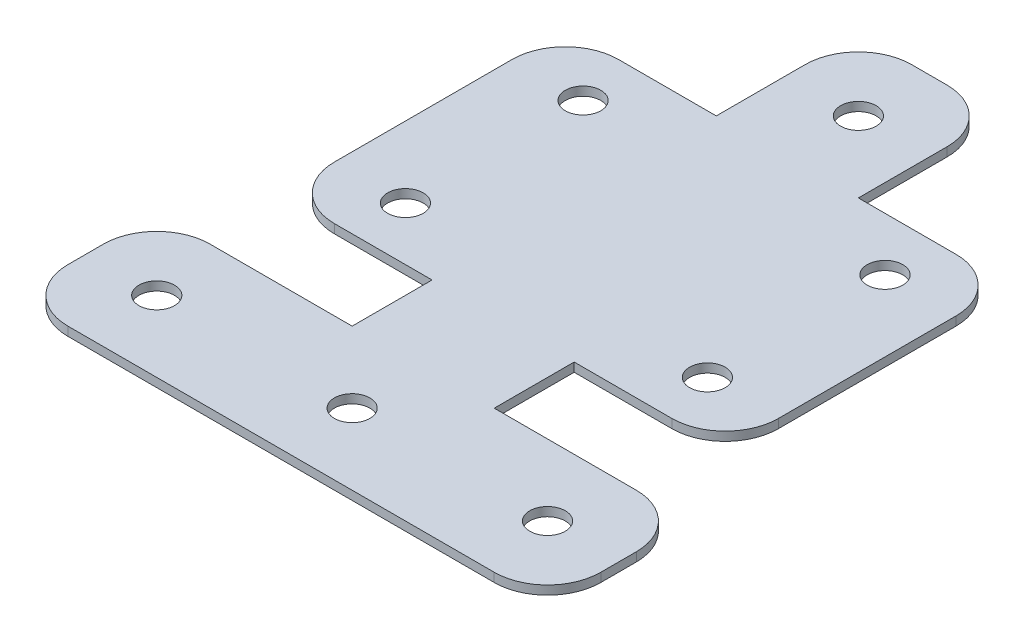
SolidWorks part; units mm, degrees
ref_plane "Front Plane" through (0, 0, 0) normal (0, 0, 1) x (1, 0, 0)
ref_plane "Top Plane" through (0, 0, 0) normal (0, 1, 0) x (1, 0, 0)
ref_plane "Right Plane" through (0, 0, 0) normal (1, 0, 0) x (0, 0, -1)
sketch "Sketch1" plane through (0, 0, 0) normal (0, 1, 0) x (1, 0, 0)
  line L0 (12.7, 12.7) -> (14.2875, 12.7)
  line L1 (-12.7, -12.7) -> (12.7, -12.7)
  line L2 (-12.7, -12.7) -> (-12.7, 12.7) construction
  line L3 (-12.7, 12.7) -> (12.7, 12.7) construction
  line L4 (12.7, -12.7) -> (12.7, 12.7) construction
  line L5 (-12.7, -12.7) -> (12.7, 12.7) construction
  line L6 (-12.7, 12.7) -> (12.7, -12.7) construction
  line L7 (22.225, 12.7) -> (47.625, 12.7)
  line L8 (47.625, 12.7) -> (47.625, -12.7)
  line L9 (47.625, -12.7) -> (22.225, -12.7)
  line L10 (22.225, -12.7) -> (12.7, -12.7)
  line L11 (22.225, 12.7) -> (22.225, -12.7) construction
  line L12 (-12.7, -12.7) -> (-22.225, -12.7)
  line L13 (-22.225, -12.7) -> (-22.225, 12.7) construction
  line L14 (-22.225, 12.7) -> (-12.7, 12.7)
  line L15 (-22.225, 12.7) -> (-47.625, 12.7)
  line L16 (-47.625, 12.7) -> (-47.625, -12.7)
  line L17 (-47.625, -12.7) -> (-22.225, -12.7)
  line L18 (-47.625, 12.7) -> (-22.225, -12.7) construction
  line L19 (-47.625, -12.7) -> (-22.225, 12.7) construction
  line L20 (22.225, 12.7) -> (47.625, -12.7) construction
  line L21 (22.225, -12.7) -> (47.625, 12.7) construction
  line L22 (-12.7, 12.7) -> (-12.7, 25.4)
  line L23 (-12.7, 26.9875) -> (12.7, 26.9875) construction
  line L24 (-12.7, 25.4) -> (12.7, 25.4) construction
  line L25 (-12.7, 26.9875) -> (-12.7, 77.7875) construction
  line L26 (-12.7, 77.7875) -> (12.7, 77.7875) construction
  line L27 (12.7, 77.7875) -> (12.7, 26.9875) construction
  line L28 (-12.7, 77.7875) -> (-12.7, 103.1875)
  line L29 (-12.7, 103.1875) -> (12.7, 103.1875)
  line L30 (12.7, 103.1875) -> (12.7, 77.7875)
  line L31 (12.7, 77.7875) -> (14.2875, 77.7875)
  line L32 (14.2875, 77.7875) -> (14.2875, 26.9875) construction
  line L33 (14.2875, 26.9875) -> (12.7, 26.9875)
  line L34 (14.2875, 26.9875) -> (39.6875, 26.9875)
  line L35 (39.6875, 26.9875) -> (39.6875, 77.7875)
  line L36 (39.6875, 77.7875) -> (14.2875, 77.7875)
  line L37 (26.9875, 77.7875) -> (26.9875, 26.9875) construction
  line L38 (-12.7, 26.9875) -> (-14.2875, 26.9875)
  line L39 (-14.2875, 26.9875) -> (-14.2875, 77.7875) construction
  line L40 (-14.2875, 77.7875) -> (-12.7, 77.7875)
  line L41 (-14.2875, 77.7875) -> (-39.6875, 77.7875)
  line L42 (-39.6875, 77.7875) -> (-39.6875, 26.9875)
  line L43 (-39.6875, 26.9875) -> (-14.2875, 26.9875)
  line L44 (-26.9875, 77.7875) -> (-26.9875, 26.9875) construction
  line L45 (12.7, 25.4) -> (12.7, 12.7)
  line L46 (-12.7, 25.4) -> (-12.7, 26.9875)
  line L47 (12.7, 26.9875) -> (12.7, 25.4)
  line L48 (14.2875, 12.7) -> (14.2875, -12.7) construction
  line L49 (20.6375, 12.7) -> (20.6375, -12.7) construction
  line L50 (14.2875, 12.7) -> (20.6375, 12.7)
  line L51 (20.6375, 12.7) -> (22.225, 12.7)
  line L52 (-12.7, 103.1875) -> (12.7, 77.7875) construction
  line L53 (12.7, 103.1875) -> (-12.7, 77.7875) construction
  circle A0 centre (26.9875, 36.5125) radius 3.175
  circle A1 centre (26.9875, 68.2625) radius 3.175
  circle A2 centre (0, 90.4875) radius 3.175
  circle A3 centre (34.925, 0) radius 3.175
  circle A4 centre (0, 0) radius 3.175
  circle A5 centre (-34.925, 0) radius 3.175
  circle A6 centre (-26.9875, 68.2625) radius 3.175
  circle A7 centre (-26.9875, 36.5125) radius 3.175
  point P0 (0, 0)
  point P14 (-34.925, 0)
  point P15 (34.925, 0)
  point P39 (0, 90.4875)
  dimension "D6" = 6.35
  dimension "D1" = 1.5875
  dimension "D2" = 25.4
  dimension "D3" = 6.35
  dimension "D4" = 12.7
  dimension "D5" = 31.75
  dimension "D7" = 9.525
  dimension "D8" = 9.525
extrude "Boss-Extrude1" add sketch "Sketch1" along normal blind 1.5875
fillet "Fillet1" radius 9.525 10 edges at (-12.7, 0.7937, -103.1875) (12.7, 0.7937, -103.1875) (47.625, 0.7937, -12.7) (47.625, 0.7937, 12.7) (-47.625, 0.7937, 12.7) (-47.625, 0.7937, -12.7) (-39.6875, 0.7937, -26.9875) (-39.6875, 0.7937, -77.7875) (39.6875, 0.7937, -77.7875) (39.6875, 0.7937, -26.9875)
